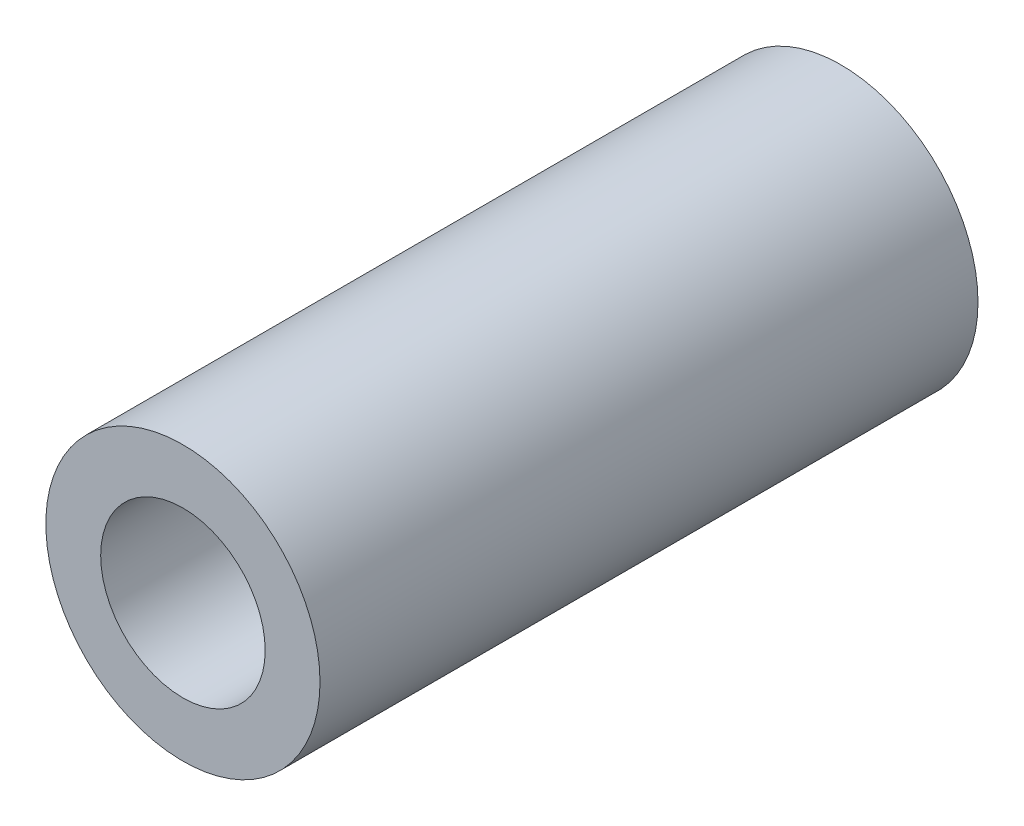
SolidWorks part; units mm, degrees
ref_plane "前视基准面" through (0, 0, 0) normal (0, 0, 1) x (1, 0, 0)
ref_plane "上视基准面" through (0, 0, 0) normal (0, 1, 0) x (1, 0, 0)
ref_plane "右视基准面" through (0, 0, 0) normal (1, 0, 0) x (0, 0, -1)
sketch "草图1" plane through (0, 0, 0) normal (0, 0, 1) x (1, 0, 0)
  circle A0 centre (0, 0) radius 1.5
  circle A1 centre (0, 0) radius 2.5
  dimension "D1" = 3
  dimension "D2" = 5
extrude "凸台-拉伸1" add sketch "草图1" along normal blind 12
